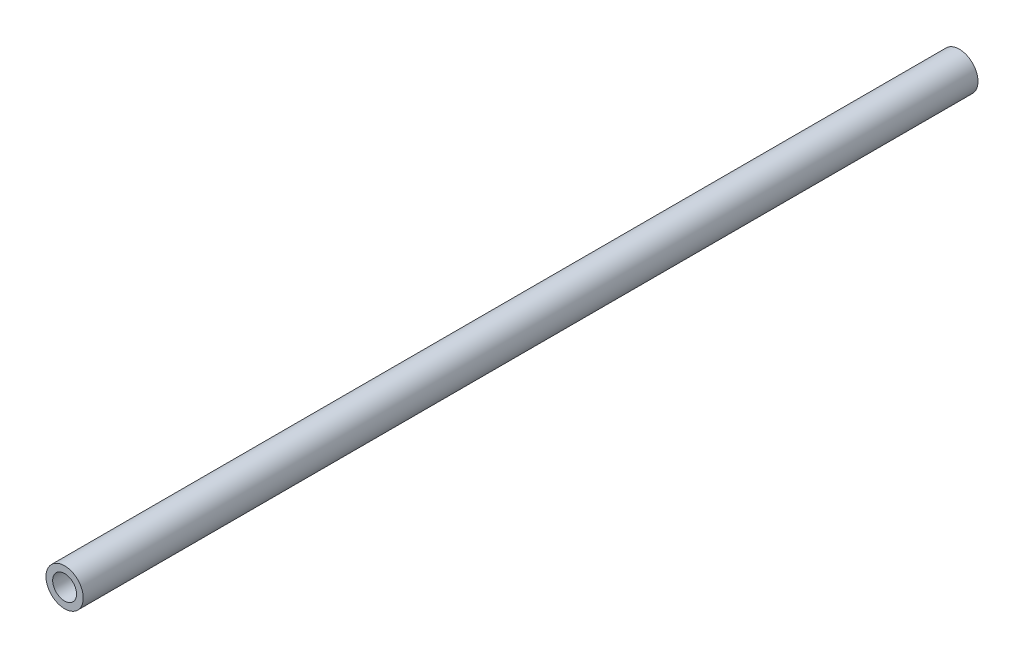
SolidWorks part; units mm, degrees
material "6063-T6，棒材(SS)"
ref_plane "前视基准面" through (0, 0, 0) normal (0, 0, 1) x (1, 0, 0)
ref_plane "上视基准面" through (0, 0, 0) normal (0, 1, 0) x (1, 0, 0)
ref_plane "右视基准面" through (0, 0, 0) normal (1, 0, 0) x (0, 0, -1)
sketch "草图1" plane through (0, 0, 0) normal (0, 0, 1) x (1, 0, 0)
  circle A0 centre (0, 0) radius 2.5
  circle A1 centre (0, 0) radius 1.6
  dimension "D1" = 5
  dimension "D2" = 3.2
extrude "凸台-拉伸1" add sketch "草图1" along normal mid plane 120
